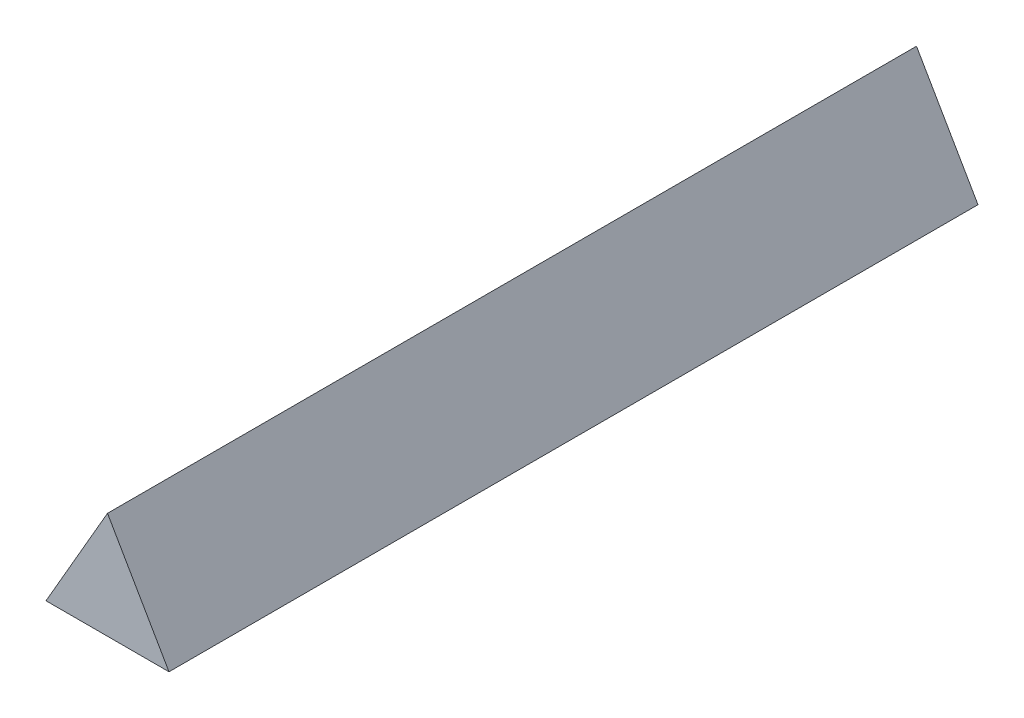
SolidWorks part; units mm, degrees
ref_plane "Front Plane" through (0, 0, 0) normal (0, 0, 1) x (1, 0, 0)
ref_plane "Top Plane" through (0, 0, 0) normal (0, 1, 0) x (1, 0, 0)
ref_plane "Right Plane" through (0, 0, 0) normal (1, 0, 0) x (0, 0, -1)
sketch "Sketch1" plane through (0, 0, 0) normal (0, 0, 1) x (1, 0, 0)
  line L0 (4.5611, 0) -> (0, 7.9)
  line L1 (0, 7.9) -> (-4.5611, 0)
  line L2 (-4.5611, 0) -> (4.5611, 0)
  dimension "D1" = 7.9
extrude "Boss-Extrude1" add sketch "Sketch1" along normal blind 60
